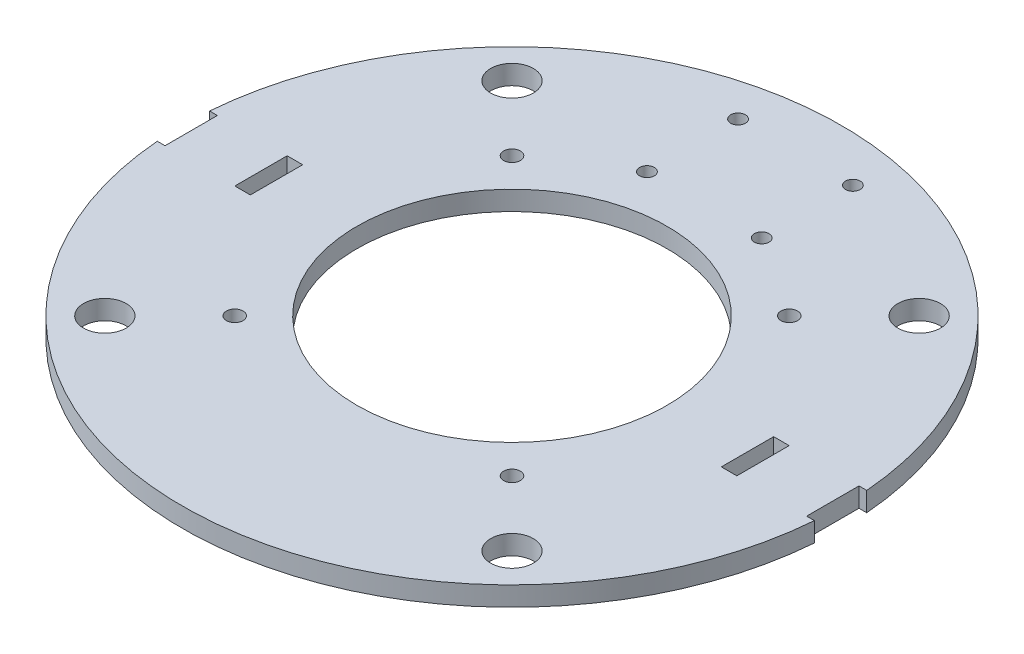
SolidWorks part; units mm, degrees
ref_plane "Front Plane" through (0, 0, 0) normal (0, 0, 1) x (1, 0, 0)
ref_plane "Top Plane" through (0, 0, 0) normal (0, 1, 0) x (1, 0, 0)
ref_plane "Right Plane" through (0, 0, 0) normal (1, 0, 0) x (0, 0, -1)
sketch "Sketch1" plane through (0, 0, 0) normal (0, 1, 0) x (1, 0, 0)
  line L0 (0, 85) -> (0, -85) construction
  line L1 (-85, 0) -> (85, 0) construction
  circle A0 centre (0, 0) radius 85
  dimension "D1" = 170
extrude "Base" add sketch "Sketch1" along normal blind 5
sketch "Sketch2" plane through (0, 5, 0) normal (0, 1, 0) x (1, 0, 0)
  line L0 (0, 85) -> (0, -85) construction
  line L1 (-85, 0) -> (85, 0) construction
  line L2 (84.7316, 6.75) -> (82.7316, 6.75)
  line L3 (82.7316, 6.75) -> (82.7316, -6.75)
  line L6 (64.7316, 6.75) -> (60.7316, 6.75)
  line L7 (64.7316, 6.75) -> (64.7316, -6.75)
  line L9 (60.7316, 6.75) -> (60.7316, -6.75)
  line L10 (84.7316, -6.75) -> (82.7316, -6.75)
  line L11 (64.7316, -6.75) -> (60.7316, -6.75)
  line L12 (-84.7316, -6.75) -> (-82.7316, -6.75)
  line L13 (-84.7316, 6.75) -> (-82.7316, 6.75)
  line L14 (-82.7316, 6.75) -> (-82.7316, -6.75)
  line L15 (-64.7316, 6.75) -> (-60.7316, 6.75)
  line L16 (-60.7316, 6.75) -> (-60.7316, -6.75)
  line L17 (-64.7316, -6.75) -> (-60.7316, -6.75)
  line L18 (-64.7316, 6.75) -> (-64.7316, -6.75)
  circle A0 centre (0, 0) radius 85 construction
  point P15 (83.7316, 6.75)
  point P16 (83.7316, -6.75)
  point P19 (82.7316, 0)
  point P20 (64.7316, 0)
  point P21 (60.7316, 0)
  circle M11 centre (0, 0) radius 85
  dimension "D1" = 6.75
  dimension "D2" = 2
  dimension "D3" = 18
  dimension "D4" = 6.75
  dimension "D5" = 4
extrude "Main Wheel Slots" cut sketch "Sketch2" against normal up to next contours L11 L7 L6 L9 | L10 L2 L3 M11 | L14 L13 L12 M11 | L16 L17 L18 L15
sketch "Sketch3" plane through (0, 5, 0) normal (0, 1, 0) x (1, 0, 0)
  line L0 (0, 85) -> (0, -85) construction
  line L1 (-82.7316, 0) -> (82.7316, 0) construction
  line L2 (-82.7316, 6.75) -> (-82.7316, -6.75) construction
  line L3 (82.7316, 6.75) -> (82.7316, -6.75) construction
  arc A0 (84.7316, 6.75) -> (-84.7316, 6.75) centre (0, 0) ccw construction
  arc A1 (-84.7316, -6.75) -> (84.7316, -6.75) centre (0, 0) ccw construction
  circle A2 centre (14.8, 73.1) radius 1.9
  circle A3 centre (14.8, 49.6) radius 1.9
  circle A4 centre (-14.8, 49.6) radius 1.9
  circle A5 centre (-14.8, 73.1) radius 1.9
  dimension "D1" = 3.8
  dimension "D3" = 10
  dimension "D4" = 3.8
  dimension "D2" = 14.8
  dimension "D5" = 14.8
  dimension "D6" = 23.5
extrude "3rd Wheel Holes" cut sketch "Sketch3" against normal up to next
sketch "Sketch6" plane through (0, 5, 0) normal (0, 1, 0) x (1, 0, 0)
  line L0 (0, 85) -> (0, -85) construction
  line L1 (-82.7316, 0) -> (82.7316, 0) construction
  line L2 (-82.7316, 6.75) -> (-82.7316, -6.75) construction
  line L3 (82.7316, 6.75) -> (82.7316, -6.75) construction
  arc A0 (84.7316, 6.75) -> (-84.7316, 6.75) centre (0, 0) ccw construction
  arc A1 (-84.7316, -6.75) -> (84.7316, -6.75) centre (0, 0) ccw construction
  circle A2 centre (35.75, 35.75) radius 2.15
  circle A3 centre (-35.75, 35.75) radius 2.15
  circle A4 centre (35.75, -35.75) radius 2.15
  circle A5 centre (-35.75, -35.75) radius 2.15
  dimension "D1" = 4.3
  dimension "D2" = 35.75
  dimension "D3" = 35.75
extrude "Fan Screw Holes" cut sketch "Sketch6" against normal blind 6
sketch "Sketch7" plane through (0, 5, 0) normal (0, 1, 0) x (1, 0, 0)
  circle A0 centre (0, 0) radius 40
  dimension "D1" = 80
extrude "Fan Blade Hole" cut sketch "Sketch7" against normal blind 6
sketch "Sketch8" plane through (0, 5, 0) normal (0, 1, 0) x (1, 0, 0)
  line L0 (0, 85) -> (0, -85) construction
  line L1 (-82.7316, 0) -> (82.7316, 0) construction
  line L2 (-82.7316, 6.75) -> (-82.7316, -6.75) construction
  line L3 (82.7316, 6.75) -> (82.7316, -6.75) construction
  arc A0 (84.7316, 6.75) -> (-84.7316, 6.75) centre (0, 0) ccw construction
  arc A1 (-84.7316, -6.75) -> (84.7316, -6.75) centre (0, 0) ccw construction
  circle A2 centre (52.5, 52.5) radius 5.5
  circle A3 centre (-52.5, 52.5) radius 5.5
  circle A4 centre (52.5, -52.5) radius 5.5
  circle A5 centre (-52.5, -52.5) radius 5.5
  dimension "D1" = 11
  dimension "D3" = 52.5
  dimension "D2" = 52.5
extrude "Bolt Holes" cut sketch "Sketch8" against normal up to next
